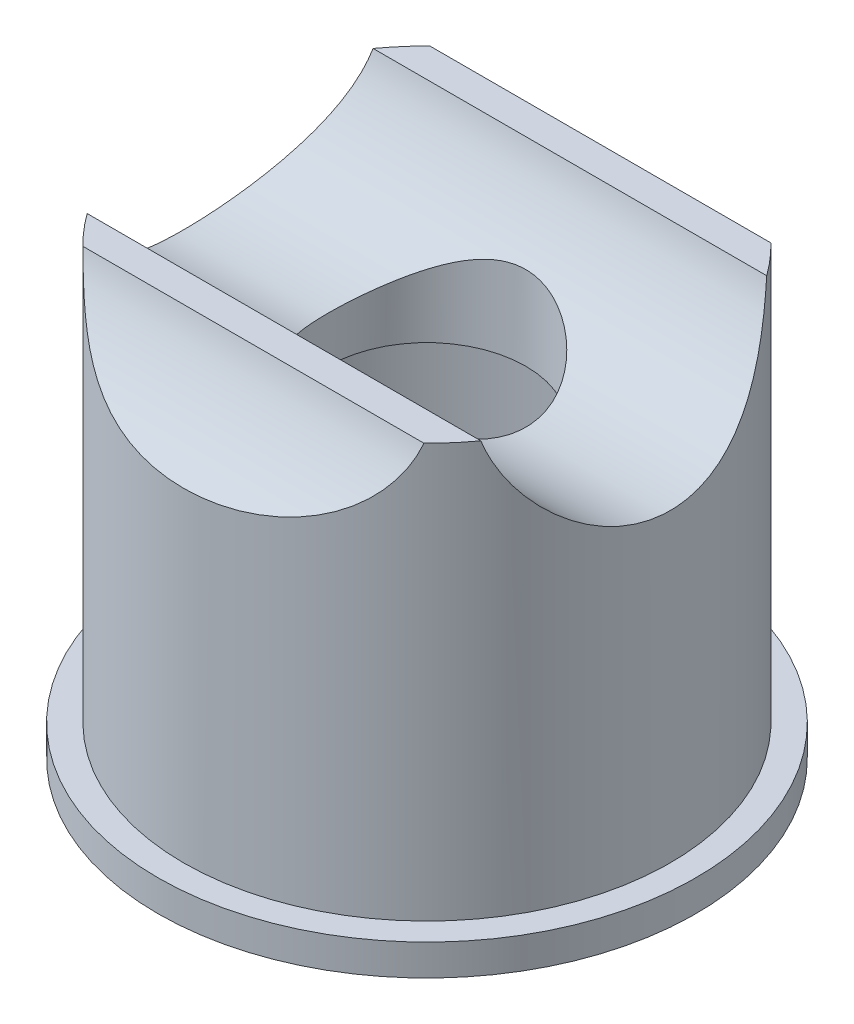
SolidWorks part; units mm, degrees
material "AISI 304"
ref_plane "Front Plane" through (0, 0, 0) normal (0, 0, 1) x (1, 0, 0)
ref_plane "Top Plane" through (0, 0, 0) normal (0, 1, 0) x (1, 0, 0)
ref_plane "Right Plane" through (0, 0, 0) normal (1, 0, 0) x (0, 0, -1)
sketch "Sketch1" plane through (0, 0, 0) normal (0, 1, 0) x (1, 0, 0)
  circle A0 centre (0, 0) radius 8.636
  dimension "D1" = 17.272
extrude "Boss-Extrude1" add sketch "Sketch1" along normal blind 14.2875
sketch "Sketch5" plane through (0, 0, 0) normal (1, 0, 0) x (0, 0, -1)
  line L0 (8.636, 14.2875) -> (-8.636, 14.2875) construction
  circle A0 centre (0, 15.5575) radius 4.7625
  circle A1 centre (-10.16, 15.5575) radius 4.7625
  circle A2 centre (10.16, 15.5575) radius 4.7625
  dimension "D1" = 9.525
  dimension "D2" = 10.16
  dimension "D3" = 10.16
  dimension "D4" = 1.27
extrude "Cut-Extrude4" cut sketch "Sketch5" against normal through all and the other way through all
sketch "Sketch2" plane through (0, 14.2875, 0) normal (0, 1, 0) x (1, 0, 0)
  circle A0 centre (0, 0) radius 7.8105
  dimension "D1" = 15.621
extrude "Cut-Extrude1" cut sketch "Sketch2" against normal offset from surface (13.2875 mm away) 1 flip side to cut up to face at (0, 0, 8.636)
sketch "Sketch4" plane through (0, 14.2875, 0) normal (0, 1, 0) x (1, 0, 0)
  circle A0 centre (0, 0) radius 3.175
  dimension "D1" = 6.35
extrude "Cut-Extrude3" cut sketch "Sketch4" against normal through all
sketch "Sketch3" plane through (0, 0, 0) normal (0, -1, 0) x (1, 0, 0)
  circle A0 centre (0, 0) radius 6.7818
  dimension "D1" = 13.5636
extrude "Cut-Extrude2" cut sketch "Sketch3" against normal offset from surface (9.3188 mm away) 4.9688 up to face at (0, 14.2875, -5.0888)
fillet "Fillet1" radius 1 1 edges at (0, 0, -6.7818)
